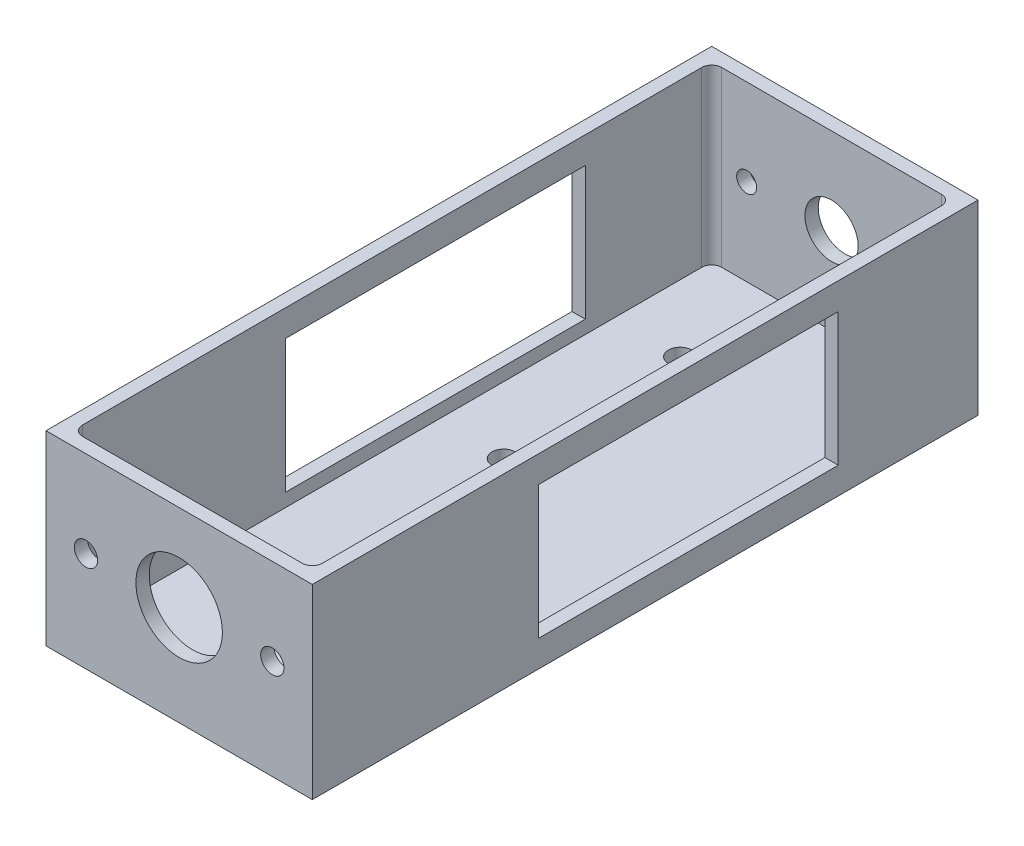
SolidWorks part; units mm, degrees
material "合金钢"
ref_plane "前视基准面" through (0, 0, 0) normal (0, 0, 1) x (1, 0, 0)
ref_plane "上视基准面" through (0, 0, 0) normal (0, 1, 0) x (1, 0, 0)
ref_plane "右视基准面" through (0, 0, 0) normal (1, 0, 0) x (0, 0, -1)
sketch "草图1" plane through (0, 0, 0) normal (0, 0, 1) x (1, 0, 0)
  line L1 (-40, -28) -> (40, -28)
  line L2 (-40, -28) -> (-40, 28)
  line L3 (-40, 28) -> (40, 28)
  line L4 (40, -28) -> (40, 28)
  line L5 (-40, -28) -> (40, 28) construction
  line L6 (-40, 28) -> (40, -28) construction
  point P0 (0, 0)
  dimension "D1" = 80
  dimension "D2" = 56
extrude "凸台-拉伸1" add sketch "草图1" against normal blind 200
sketch "草图2" plane through (0, 28, 0) normal (0, 1, 0) x (1, 0, 0)
  line L0 (-36, 193) -> (-36, 7)
  line L1 (-33, 4) -> (33, 4)
  line L2 (36, 7) -> (36, 193)
  line L3 (33, 196) -> (-33, 196)
  line L4 (-40, 0) -> (40, 0)
  line L5 (40, 0) -> (40, 200)
  line L6 (40, 200) -> (-40, 200)
  line L7 (-40, 200) -> (-40, 0)
  line L8 (-40, 0) -> (40, 0)
  line L9 (40, 0) -> (40, 200)
  line L10 (40, 200) -> (-40, 200)
  line L11 (-40, 200) -> (-40, 0)
  line L12 (-36, 4) -> (36, 4) construction
  line L13 (36, 4) -> (36, 196) construction
  line L14 (-36, 196) -> (-36, 4) construction
  line L15 (36, 196) -> (-36, 196) construction
  arc A0 (33, 4) -> (36, 7) centre (33, 7) ccw
  arc A1 (-36, 7) -> (-33, 4) centre (-33, 7) ccw
  arc A2 (36, 193) -> (33, 196) centre (33, 193) ccw
  arc A3 (-36, 193) -> (-33, 196) centre (-33, 193) cw
  dimension "D3" = 3
  dimension "D1" = 0
  dimension "D2" = 4
extrude "切除-拉伸1" cut sketch "草图2" against normal blind 52 contours A3 L0 A1 L1 A0 L2 A2 L3
sketch "草图3" plane through (0, 0, 0) normal (0, 0, 1) x (1, 0, 0)
  line L0 (0, 0) -> (0, 37.0041) construction
  line L4 (-40, -28) -> (40, -28) construction
  line L5 (40, 28) -> (-40, 28) construction
  line L9 (0, 2) -> (0, 28) construction
  line L10 (-28, 2) -> (28, 2) construction
  circle A0 centre (-28, 2) radius 3.5
  circle A1 centre (0, 2) radius 13
  circle A2 centre (28, 2) radius 3.5
  dimension "D2" = 7
  dimension "D3" = 26
  dimension "D4" = 7
  dimension "D5" = 30
  dimension "D6" = 28
  dimension "D7" = 28
extrude "切除-拉伸2" cut sketch "草图3" against normal blind 10
sketch "草图5" plane through (0, 0, -200) normal (0, 0, -1) x (-1, 0, 0)
  line L0 (0, -25.8214) -> (0, 19.1786) construction
  line L1 (0, 28) -> (0, 39.9128) construction
  line L2 (0, 2) -> (25.5, 2) construction
  line L3 (40, -28) -> (-40, -28) construction
  line L5 (-40, 28) -> (40, 28) construction
  circle A0 centre (0, 2) radius 8
  circle A1 centre (25.5, 2) radius 3
  circle A2 centre (-25.5, 2) radius 3
  dimension "D1" = 16
  dimension "D3" = 6
  dimension "D2" = 30
  dimension "D4" = 25.5
extrude "切除-拉伸4" cut sketch "草图5" against normal blind 10
sketch "草图6" plane through (0, -24, 0) normal (0, 1, 0) x (1, 0, 0)
  line L0 (-16, 113.5) -> (-16, 166.5) construction
  line L1 (-16, 140) -> (-23.7867, 140) construction
  line L2 (-36, 193) -> (-36, 7) construction
  line L4 (-40, 200) -> (40, 200) construction
  circle A0 centre (-16, 166.5) radius 3.5
  circle A1 centre (-16, 113.5) radius 3.5
  dimension "D2" = 7
  dimension "D5" = 7
  dimension "D1" = 53
  dimension "D3" = 20
  dimension "D4" = 60
extrude "切除-拉伸5" cut sketch "草图6" against normal blind 10
sketch "草图7" plane through (-40, 0, 0) normal (-1, 0, 0) x (0, 0, 1)
  line L1 (-158.0147, -20) -> (-68.0147, -20)
  line L2 (-158.0147, -20) -> (-158.0147, 20)
  line L3 (-158.0147, 20) -> (-68.0147, 20)
  line L4 (-68.0147, -20) -> (-68.0147, 20)
  line L5 (-158.0147, -20) -> (-68.0147, 20) construction
  line L6 (-158.0147, 20) -> (-68.0147, -20) construction
  line L7 (-200, 28) -> (-200, -28) construction
  point P0 (-113.0147, 0)
  point P5 (0, 0)
  point P11 (-200, 0)
  point P12 (0, 0)
  point P13 (0, 0)
  point P14 (-113.0147, 0)
  dimension "D1" = 90
  dimension "D2" = 40
extrude "切除-拉伸6" cut sketch "草图7" against normal through all
